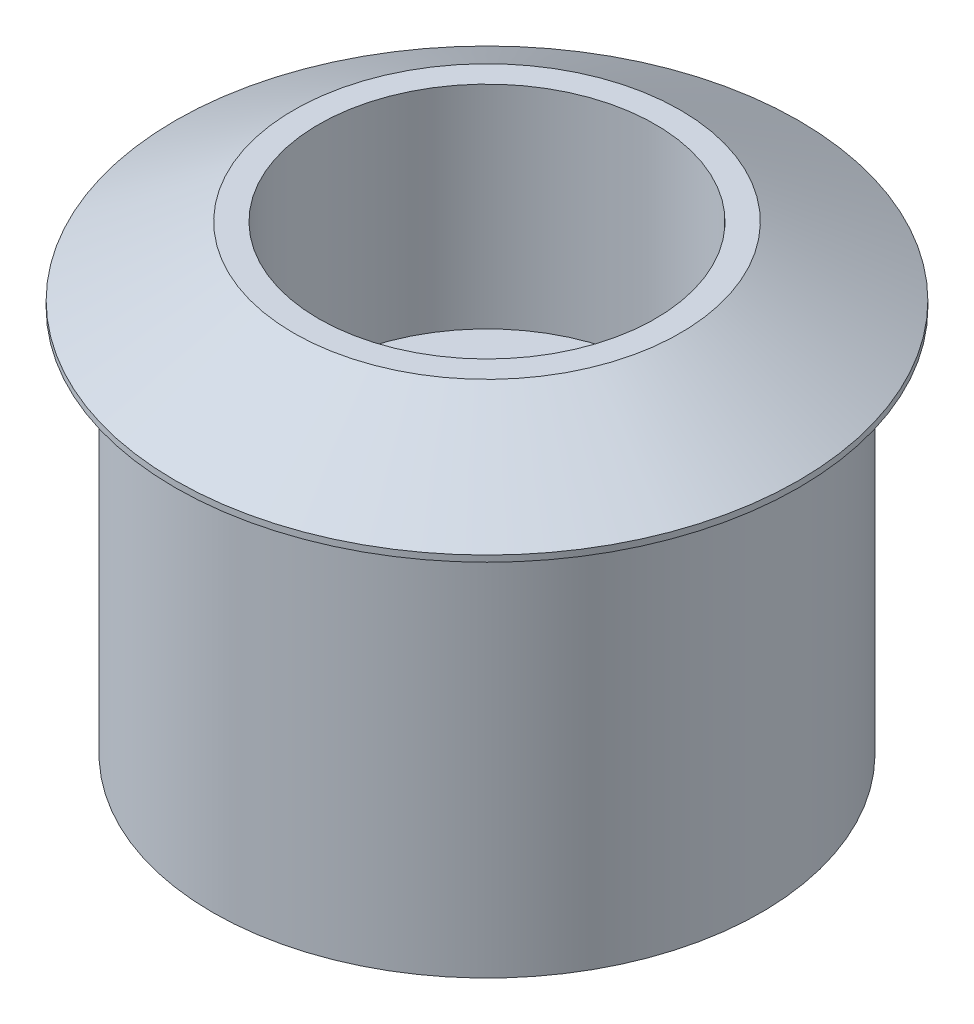
SolidWorks part; units mm, degrees
material "Alliage 1060"
ref_plane "Plan de face" through (0, 0, 0) normal (0, 0, 1) x (1, 0, 0)
ref_plane "Plan de dessus" through (0, 0, 0) normal (0, 1, 0) x (1, 0, 0)
ref_plane "Plan de droite" through (0, 0, 0) normal (1, 0, 0) x (0, 0, -1)
sketch "Esquisse1" plane through (0, 0, 0) normal (0, 0, 1) x (1, 0, 0)
  line L0 (4.1, 0) -> (4.1, 9.9924)
  line L1 (4.1, 0) -> (11, 0)
  line L2 (11, 0) -> (11, 15.5)
  line L3 (0, 10.7305) -> (0, -2.4344) construction
  line L4 (11, 15.5) -> (12.5, 15.5)
  line L5 (6.75, 18.4924) -> (7.75, 18.4924)
  line L6 (4.1, 9.9924) -> (6.75, 9.9924)
  line L7 (6.75, 9.9924) -> (6.75, 18.4924)
  line L8 (7.75, 18.4924) -> (12.5, 15.75)
  line L9 (12.5, 15.5) -> (12.5, 15.75)
  dimension "D1" = 6.75
  dimension "D2" = 11
  dimension "D3" = 1
  dimension "D4" = 15.5
  dimension "D5" = 12.5
  dimension "D6" = 8.5
  dimension "D7" = 30
  dimension "D8" = 8.2
  dimension "D9" = 0.25
revolve "Révolution1" add sketch "Esquisse1" angle 360 about L3
